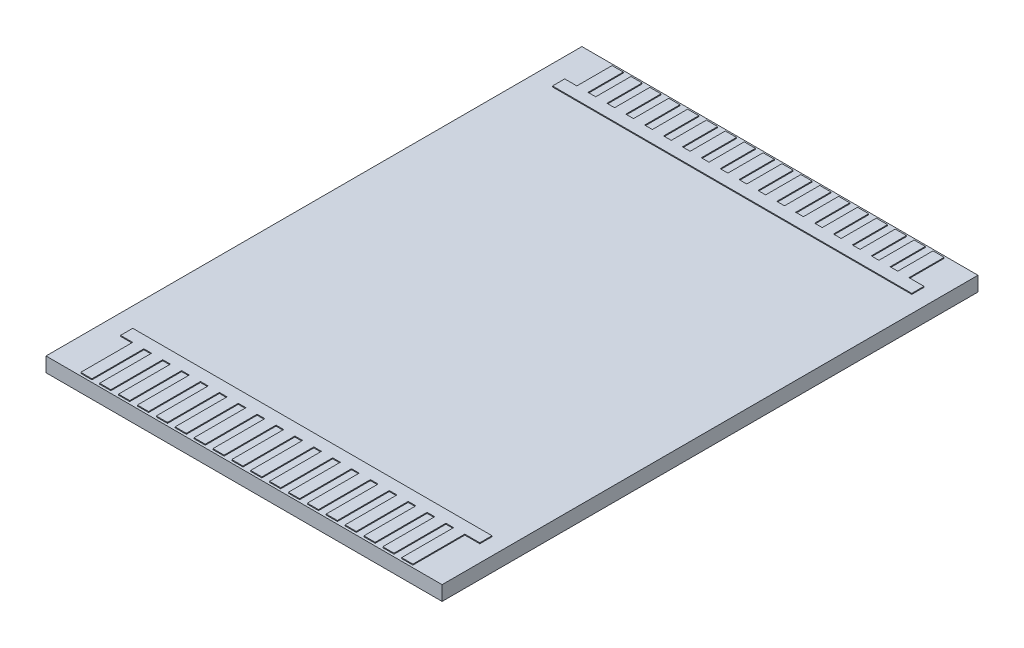
SolidWorks part; units mm, degrees
ref_plane "Front Plane" through (0, 0, 0) normal (0, 0, 1) x (1, 0, 0)
ref_plane "Top Plane" through (0, 0, 0) normal (0, 1, 0) x (1, 0, 0)
ref_plane "Right Plane" through (0, 0, 0) normal (1, 0, 0) x (0, 0, -1)
sketch "Sketch1" plane through (0, 0, 0) normal (0, 1, 0) x (1, 0, 0)
  line L1 (0, 0) -> (43.18, 0)
  line L2 (0, 0) -> (0, 58.42)
  line L3 (0, 58.42) -> (43.18, 58.42)
  line L4 (43.18, 0) -> (43.18, 58.42)
extrude "Boss-Extrude1" add sketch "Sketch1" along normal blind 1.5875
sketch "Sketch2" plane through (0, 1.5875, 0) normal (0, 1, 0) x (1, 0, 0)
  line L0 (2.217, 54.33) -> (41.38, 54.33) construction
  line L1 (2.217, 7.24) -> (41.38, 7.24)
  line L2 (2.217, 7.24) -> (2.217, 5.91)
  line L3 (2.217, 5.91) -> (3.54, 5.91)
  line L4 (41.38, 7.24) -> (41.38, 5.91)
  line L5 (2.217, 54.33) -> (2.217, 53) construction
  line L6 (2.217, 53) -> (41.38, 53) construction
  line L7 (41.069, 54.33) -> (41.069, 53) construction
  line L8 (4.76, 5.91) -> (5.598, 5.91)
  line L9 (3.54, 0.25) -> (4.76, 0.25)
  line L10 (3.54, 0.25) -> (3.54, 5.91)
  line L11 (5.598, 0.25) -> (6.818, 0.25)
  line L12 (4.76, 0.25) -> (4.76, 5.91)
  line L13 (5.598, 0.25) -> (5.598, 5.91)
  line L14 (6.818, 0.25) -> (6.818, 5.91)
  line L15 (7.656, 0.25) -> (8.876, 0.25)
  line L16 (7.656, 0.25) -> (7.656, 5.91)
  line L17 (8.876, 0.25) -> (8.876, 5.91)
  line L18 (9.714, 0.25) -> (10.934, 0.25)
  line L19 (9.714, 0.25) -> (9.714, 5.91)
  line L20 (10.934, 0.25) -> (10.934, 5.91)
  line L21 (11.772, 0.25) -> (12.992, 0.25)
  line L22 (11.772, 0.25) -> (11.772, 5.91)
  line L23 (12.992, 0.25) -> (12.992, 5.91)
  line L24 (13.83, 0.25) -> (15.05, 0.25)
  line L25 (13.83, 0.25) -> (13.83, 5.91)
  line L26 (15.05, 0.25) -> (15.05, 5.91)
  line L27 (15.888, 0.25) -> (17.108, 0.25)
  line L28 (15.888, 0.25) -> (15.888, 5.91)
  line L29 (17.108, 0.25) -> (17.108, 5.91)
  line L30 (17.946, 0.25) -> (19.166, 0.25)
  line L31 (17.946, 0.25) -> (17.946, 5.91)
  line L32 (19.166, 0.25) -> (19.166, 5.91)
  line L33 (20.004, 0.25) -> (21.224, 0.25)
  line L34 (20.004, 0.25) -> (20.004, 5.91)
  line L35 (21.224, 0.25) -> (21.224, 5.91)
  line L36 (22.062, 0.25) -> (23.282, 0.25)
  line L37 (22.062, 0.25) -> (22.062, 5.91)
  line L38 (23.282, 0.25) -> (23.282, 5.91)
  line L39 (24.12, 0.25) -> (25.34, 0.25)
  line L40 (24.12, 0.25) -> (24.12, 5.91)
  line L41 (25.34, 0.25) -> (25.34, 5.91)
  line L42 (26.178, 0.25) -> (27.398, 0.25)
  line L43 (26.178, 0.25) -> (26.178, 5.91)
  line L44 (27.398, 0.25) -> (27.398, 5.91)
  line L45 (41.38, 53) -> (2.217, 53)
  line L46 (41.38, 53) -> (41.38, 54.33)
  line L47 (41.38, 54.33) -> (39.746, 54.33)
  line L48 (28.236, 0.25) -> (29.456, 0.25)
  line L49 (28.236, 0.25) -> (28.236, 5.91)
  line L50 (29.456, 0.25) -> (29.456, 5.91)
  line L51 (30.294, 0.25) -> (31.514, 0.25)
  line L52 (30.294, 0.25) -> (30.294, 5.91)
  line L53 (31.514, 0.25) -> (31.514, 5.91)
  line L54 (32.352, 0.25) -> (33.572, 0.25)
  line L55 (32.352, 0.25) -> (32.352, 5.91)
  line L56 (33.572, 0.25) -> (33.572, 5.91)
  line L57 (34.41, 0.25) -> (35.63, 0.25)
  line L58 (34.41, 0.25) -> (34.41, 5.91)
  line L59 (35.63, 0.25) -> (35.63, 5.91)
  line L60 (36.468, 0.25) -> (37.688, 0.25)
  line L61 (36.468, 0.25) -> (36.468, 5.91)
  line L62 (37.688, 0.25) -> (37.688, 5.91)
  line L63 (6.818, 5.91) -> (7.656, 5.91)
  line L64 (8.876, 5.91) -> (9.714, 5.91)
  line L65 (10.934, 5.91) -> (11.772, 5.91)
  line L66 (12.992, 5.91) -> (13.83, 5.91)
  line L67 (15.05, 5.91) -> (15.888, 5.91)
  line L68 (17.108, 5.91) -> (17.946, 5.91)
  line L69 (19.166, 5.91) -> (20.004, 5.91)
  line L70 (21.224, 5.91) -> (22.062, 5.91)
  line L71 (23.282, 5.91) -> (24.12, 5.91)
  line L72 (25.34, 5.91) -> (26.178, 5.91)
  line L73 (27.398, 5.91) -> (28.236, 5.91)
  line L74 (29.456, 5.91) -> (30.294, 5.91)
  line L75 (31.514, 5.91) -> (32.352, 5.91)
  line L76 (33.572, 5.91) -> (34.41, 5.91)
  line L77 (35.63, 5.91) -> (36.468, 5.91)
  line L78 (37.688, 5.91) -> (38.526, 5.91)
  line L79 (39.746, 5.91) -> (41.38, 5.91)
  line L80 (2.217, 53) -> (2.217, 54.33)
  line L81 (38.526, 54.33) -> (37.688, 54.33)
  line L82 (39.746, 58.17) -> (38.526, 58.17)
  line L83 (39.746, 58.17) -> (39.746, 54.33)
  line L84 (37.688, 58.17) -> (36.468, 58.17)
  line L85 (38.526, 58.17) -> (38.526, 54.33)
  line L86 (37.688, 58.17) -> (37.688, 54.33)
  line L87 (36.468, 58.17) -> (36.468, 54.33)
  line L88 (35.63, 58.17) -> (34.41, 58.17)
  line L89 (35.63, 58.17) -> (35.63, 54.33)
  line L90 (34.41, 58.17) -> (34.41, 54.33)
  line L91 (33.572, 58.17) -> (32.352, 58.17)
  line L92 (33.572, 58.17) -> (33.572, 54.33)
  line L93 (38.526, 0.25) -> (39.746, 0.25)
  line L94 (38.526, 0.25) -> (38.526, 5.91)
  line L95 (39.746, 0.25) -> (39.746, 5.91)
  line L96 (32.352, 58.17) -> (32.352, 54.33)
  line L97 (31.514, 58.17) -> (30.294, 58.17)
  line L98 (31.514, 58.17) -> (31.514, 54.33)
  line L99 (30.294, 58.17) -> (30.294, 54.33)
  line L100 (29.456, 58.17) -> (28.236, 58.17)
  line L101 (29.456, 58.17) -> (29.456, 54.33)
  line L102 (28.236, 58.17) -> (28.236, 54.33)
  line L103 (27.398, 58.17) -> (26.178, 58.17)
  line L104 (27.398, 58.17) -> (27.398, 54.33)
  line L105 (26.178, 58.17) -> (26.178, 54.33)
  line L106 (25.34, 58.17) -> (24.12, 58.17)
  line L107 (25.34, 58.17) -> (25.34, 54.33)
  line L108 (24.12, 58.17) -> (24.12, 54.33)
  line L109 (23.282, 58.17) -> (22.062, 58.17)
  line L110 (23.282, 58.17) -> (23.282, 54.33)
  line L111 (22.062, 58.17) -> (22.062, 54.33)
  line L112 (21.224, 58.17) -> (20.004, 58.17)
  line L113 (21.224, 58.17) -> (21.224, 54.33)
  line L114 (20.004, 58.17) -> (20.004, 54.33)
  line L115 (19.166, 58.17) -> (17.946, 58.17)
  line L116 (19.166, 58.17) -> (19.166, 54.33)
  line L117 (17.946, 58.17) -> (17.946, 54.33)
  line L118 (17.108, 58.17) -> (15.888, 58.17)
  line L119 (17.108, 58.17) -> (17.108, 54.33)
  line L120 (15.888, 58.17) -> (15.888, 54.33)
  line L121 (15.05, 58.17) -> (13.83, 58.17)
  line L122 (15.05, 58.17) -> (15.05, 54.33)
  line L123 (13.83, 58.17) -> (13.83, 54.33)
  line L124 (12.992, 58.17) -> (11.772, 58.17)
  line L125 (12.992, 58.17) -> (12.992, 54.33)
  line L126 (11.772, 58.17) -> (11.772, 54.33)
  line L127 (10.934, 58.17) -> (9.714, 58.17)
  line L128 (10.934, 58.17) -> (10.934, 54.33)
  line L129 (9.714, 58.17) -> (9.714, 54.33)
  line L130 (8.876, 58.17) -> (7.656, 58.17)
  line L131 (8.876, 58.17) -> (8.876, 54.33)
  line L132 (7.656, 58.17) -> (7.656, 54.33)
  line L133 (6.818, 58.17) -> (5.598, 58.17)
  line L134 (6.818, 58.17) -> (6.818, 54.33)
  line L135 (5.598, 58.17) -> (5.598, 54.33)
  line L136 (36.468, 54.33) -> (35.63, 54.33)
  line L137 (34.41, 54.33) -> (33.572, 54.33)
  line L138 (32.352, 54.33) -> (31.514, 54.33)
  line L139 (30.294, 54.33) -> (29.456, 54.33)
  line L140 (28.236, 54.33) -> (27.398, 54.33)
  line L141 (26.178, 54.33) -> (25.34, 54.33)
  line L142 (24.12, 54.33) -> (23.282, 54.33)
  line L143 (22.062, 54.33) -> (21.224, 54.33)
  line L144 (20.004, 54.33) -> (19.166, 54.33)
  line L145 (17.946, 54.33) -> (17.108, 54.33)
  line L146 (15.888, 54.33) -> (15.05, 54.33)
  line L147 (13.83, 54.33) -> (12.992, 54.33)
  line L148 (11.772, 54.33) -> (10.934, 54.33)
  line L149 (9.714, 54.33) -> (8.876, 54.33)
  line L150 (7.656, 54.33) -> (6.818, 54.33)
  line L151 (5.598, 54.33) -> (4.76, 54.33)
  line L152 (3.54, 54.33) -> (2.217, 54.33)
  line L153 (4.76, 58.17) -> (3.54, 58.17)
  line L154 (4.76, 58.17) -> (4.76, 54.33)
  line L155 (3.54, 58.17) -> (3.54, 54.33)
  dimension "2.058" = 18
extrude "Boss-Extrude2" add sketch "Sketch2" along normal blind 0.1
